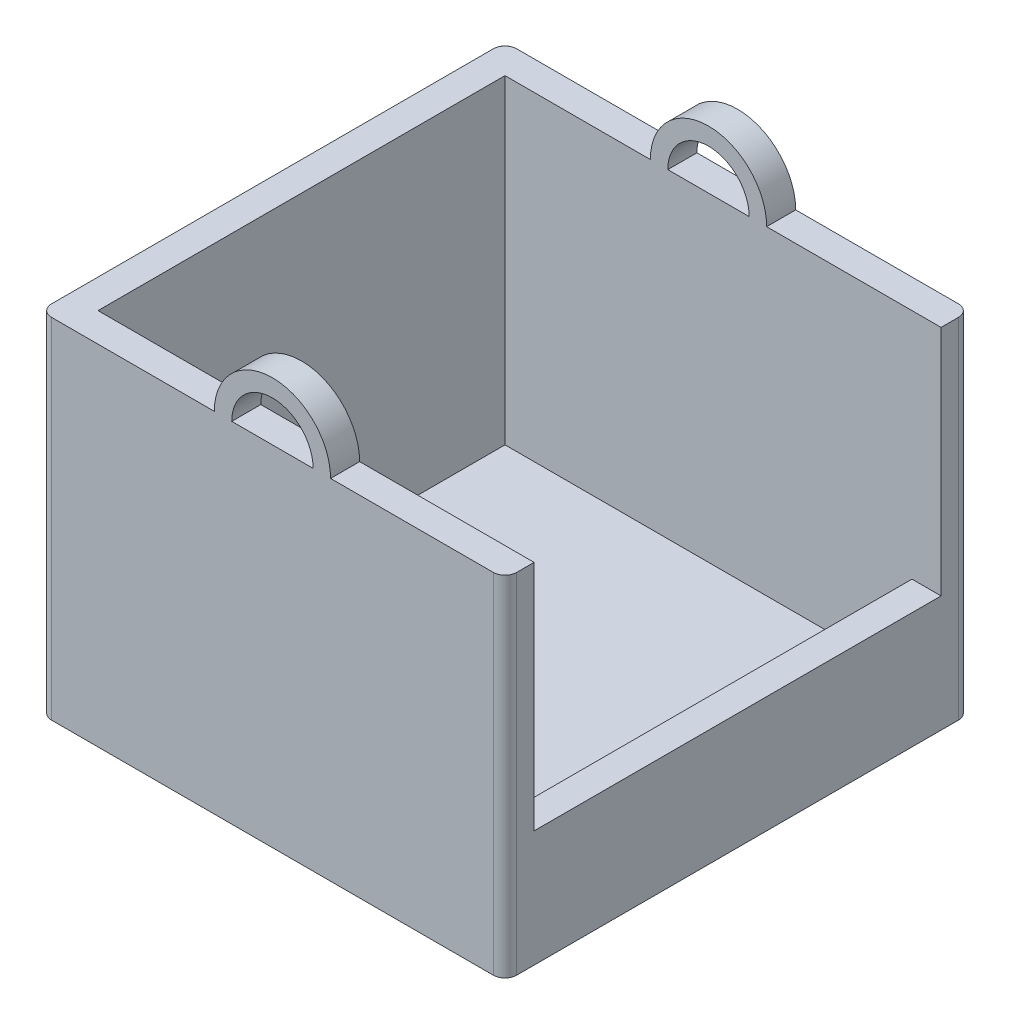
SolidWorks part; units mm, degrees
ref_plane "Front Plane" through (0, 0, 0) normal (0, 0, 1) x (1, 0, 0)
ref_plane "Top Plane" through (0, 0, 0) normal (0, 1, 0) x (1, 0, 0)
ref_plane "Right Plane" through (0, 0, 0) normal (1, 0, 0) x (0, 0, -1)
sketch "Sketch1" plane through (0, 0, 0) normal (0, 1, 0) x (1, 0, 0)
  line L1 (-20, -20) -> (20, -20)
  line L2 (-20, -20) -> (-20, 20)
  line L3 (-20, 20) -> (20, 20)
  line L4 (20, -20) -> (20, 20)
  line L5 (-20, -20) -> (20, 20) construction
  line L6 (-20, 20) -> (20, -20) construction
  line L11 (-14.645, -14.645) -> (14.645, 14.645) construction
  line L12 (-14.645, 14.645) -> (14.645, -14.645) construction
  line L13 (-17.5, -17.5) -> (17.5, -17.5)
  line L14 (-17.5, -17.5) -> (-17.5, 17.5)
  line L15 (-17.5, 17.5) -> (17.5, 17.5)
  line L16 (17.5, -17.5) -> (17.5, 17.5)
  line L17 (-17.5, -17.5) -> (17.5, 17.5) construction
  line L18 (-17.5, 17.5) -> (17.5, -17.5) construction
  point P0 (0, 0)
  point P6 (0, 0)
  point P11 (0, 0)
  dimension "D1" = 40
  dimension "D2" = 40
  dimension "D3" = 35
  dimension "D4" = 35
extrude "Boss-Extrude1" add sketch "Sketch1" along normal blind 30
sketch "Sketch2" plane through (0, 0, 0) normal (0, 1, 0) x (1, 0, 0)
  line L1 (-20, -20) -> (20, -20)
  line L2 (-20, -20) -> (-20, 20)
  line L3 (-20, 20) -> (20, 20)
  line L4 (20, -20) -> (20, 20)
  line L5 (-20, -20) -> (20, 20) construction
  line L6 (-20, 20) -> (20, -20) construction
  point P0 (0, 0)
extrude "Boss-Extrude2" add sketch "Sketch2" along normal blind 2.5
ref_plane "Plane1" through (20, 0, 0) normal (1, 0, 0) x (0, 0, -1)
sketch "Sketch3" plane through (20, 0, 0) normal (1, 0, 0) x (0, 0, -1)
  line L0 (20, 30) -> (20, 0) construction
  line L1 (-20, 30) -> (20, 30)
  line L2 (-20, 30) -> (-20, 10)
  line L3 (-20, 10) -> (20, 10)
  line L4 (20, 30) -> (20, 10)
  line L5 (-17.5, 10) -> (-17.5, 30)
  line L6 (17.5, 10) -> (17.5, 30)
  dimension "D1" = 20
  dimension "D2" = 2.5
  dimension "D3" = 2.5
extrude "Cut-Extrude1" cut sketch "Sketch3" against normal blind 2.5 contours L3 L6 L1 L5
fillet "Fillet1" radius 1 2 edges at (20, 15, 20) (-20, 15, 20)
fillet "Fillet2" radius 1 2 edges at (-20, 15, -20) (20, 15, -20)
ref_plane "Plane2" through (0, 0, 20) normal (0, 0, 1) x (1, 0, 0)
sketch "Sketch4" plane through (0, 0, 20) normal (0, 0, 1) x (1, 0, 0)
  line L0 (0, 30) -> (0, 35)
  line L1 (-19, 30) -> (19, 30) construction
  line L4 (0, 30) -> (5, 30)
  line L5 (0, 30) -> (-3.5, 30)
  line L6 (0, 30) -> (3.5, 30)
  line L7 (-5, 30) -> (-3.5, 30)
  arc A0 (-5, 30) -> (5, 30) centre (0, 30) cw
  arc A1 (-3.5, 30) -> (3.5, 30) centre (0, 30) cw
  dimension "D5" = 3.5
  dimension "D1" = 5
  dimension "D2" = 5
  dimension "D3" = 5
  dimension "D4" = 3.5
extrude "Boss-Extrude3" add sketch "Sketch4" against normal blind 2.5 contours L7 A1 L0 A0 | L0 A1 L4 A0
ref_plane "Plane4" through (0, 0, -20) normal (0, 0, -1) x (-1, 0, 0)
sketch "Sketch5" plane through (0, 0, -20) normal (0, 0, -1) x (-1, 0, 0)
  line L0 (0, 30) -> (0, 35)
  line L1 (-19, 30) -> (19, 30) construction
  line L3 (0, 30) -> (-3.5, 30)
  line L4 (0, 30) -> (3.5, 30)
  line L5 (-5, 30) -> (5, 30)
  arc A0 (-5, 30) -> (5, 30) centre (0, 30) cw
  arc A1 (-3.5, 30) -> (3.5, 30) centre (0, 30) cw
  dimension "D4" = 3.5
  dimension "D1" = 5
  dimension "D2" = 5
  dimension "D3" = 3.5
extrude "Boss-Extrude4" add sketch "Sketch5" against normal blind 2.5 contours L0 A1 L5 A0 | L5 A1 L0 A0
